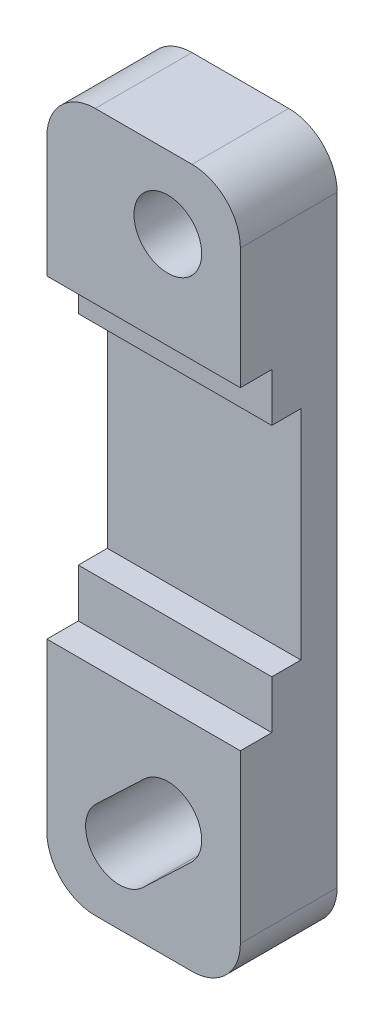
SolidWorks part; units mm, degrees
ref_plane "Front Plane" through (0, 0, 0) normal (0, 0, 1) x (1, 0, 0)
ref_plane "Top Plane" through (0, 0, 0) normal (0, 1, 0) x (1, 0, 0)
ref_plane "Right Plane" through (0, 0, 0) normal (1, 0, 0) x (0, 0, -1)
sketch "Sketch1" plane through (0, 0, 0) normal (0, 0, 1) x (1, 0, 0)
  line L6 (0, 53.4399) -> (0, -35.9992) construction
  line L7 (0.9642, -11.515) -> (-1.0358, -13.415)
  line L8 (-5, 11.5) -> (-5, -13.4)
  line L9 (1, -15.4) -> (-3, -15.4)
  line L10 (3, 11.5) -> (3, -13.4)
  line L11 (1, 13.5) -> (-3, 13.5)
  line L12 (-0.9642, -9.485) -> (-2.9642, -11.385)
  circle A0 centre (0, 10.5) radius 1.4
  arc A7 (1, 13.5) -> (3, 11.5) centre (1, 11.5) cw
  arc A8 (-3, 13.5) -> (-5, 11.5) centre (-3, 11.5) ccw
  arc A9 (-3, -15.4) -> (-5, -13.4) centre (-3, -13.4) cw
  arc A10 (3, -13.4) -> (1, -15.4) centre (1, -13.4) cw
  arc A11 (-0.9642, -9.485) -> (0.9642, -11.515) centre (0, -10.5) cw
  arc A12 (-1.0358, -13.415) -> (-2.9642, -11.385) centre (-2, -12.4) cw
  dimension "D1" = 2.8
  dimension "D4" = 10.5
  dimension "D5" = 10.5
extrude "Boss-Extrude1" add sketch "Sketch1" along normal blind 4
sketch "Sketch2" plane through (3, 0, 0) normal (1, 0, 0) x (0, 0, -1)
  line L0 (-4, -13.4) -> (-4, 11.5) construction
  line L1 (-4, 6.5) -> (-2.7, 6.5)
  line L2 (-4, 6.5) -> (-4, -6.5)
  line L3 (-4, -6.5) -> (-2.7, -6.5)
  line L4 (-2.7, 6.5) -> (-2.7, 4.5)
  line L5 (-2.7, 4.5) -> (-1.5, 4.5)
  line L6 (-1.5, 4.5) -> (-1.5, -4.5)
  line L7 (-1.5, -4.5) -> (-2.7, -4.5)
  line L8 (-2.7, -4.5) -> (-2.7, -6.5)
  point P9 (-1.5, 0)
  dimension "D1" = 6.5
  dimension "D2" = 6.5
  dimension "D3" = 1.3
  dimension "D4" = 9
  dimension "D5" = 2.5
extrude "Cut-Extrude1" cut sketch "Sketch2" against normal through all
